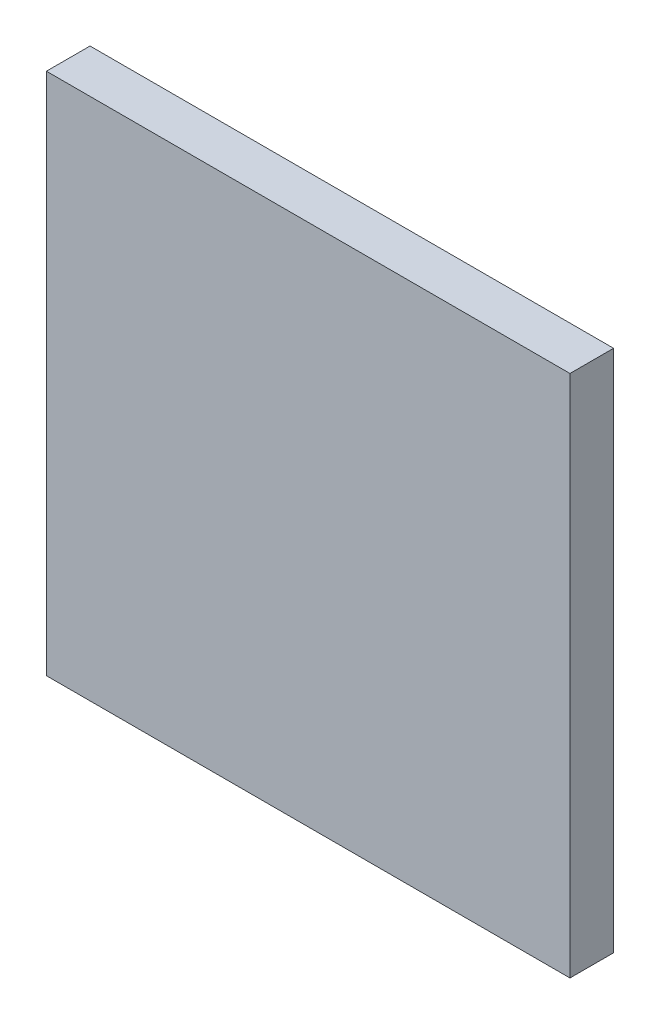
SolidWorks part; units mm, degrees
ref_plane "Front Plane" through (0, 0, 0) normal (0, 0, 1) x (1, 0, 0)
ref_plane "Top Plane" through (0, 0, 0) normal (0, 1, 0) x (1, 0, 0)
ref_plane "Right Plane" through (0, 0, 0) normal (1, 0, 0) x (0, 0, -1)
sketch "Sketch1" plane through (0, 0, 0) normal (0, 0, 1) x (1, 0, 0)
  line L1 (0, 0) -> (30, 0)
  line L2 (0, 0) -> (0, 30)
  line L3 (0, 30) -> (30, 30)
  line L4 (30, 0) -> (30, 30)
  dimension "D1" = 30
  dimension "D2" = 30
extrude "Boss-Extrude1" add sketch "Sketch1" along normal blind 2.5
